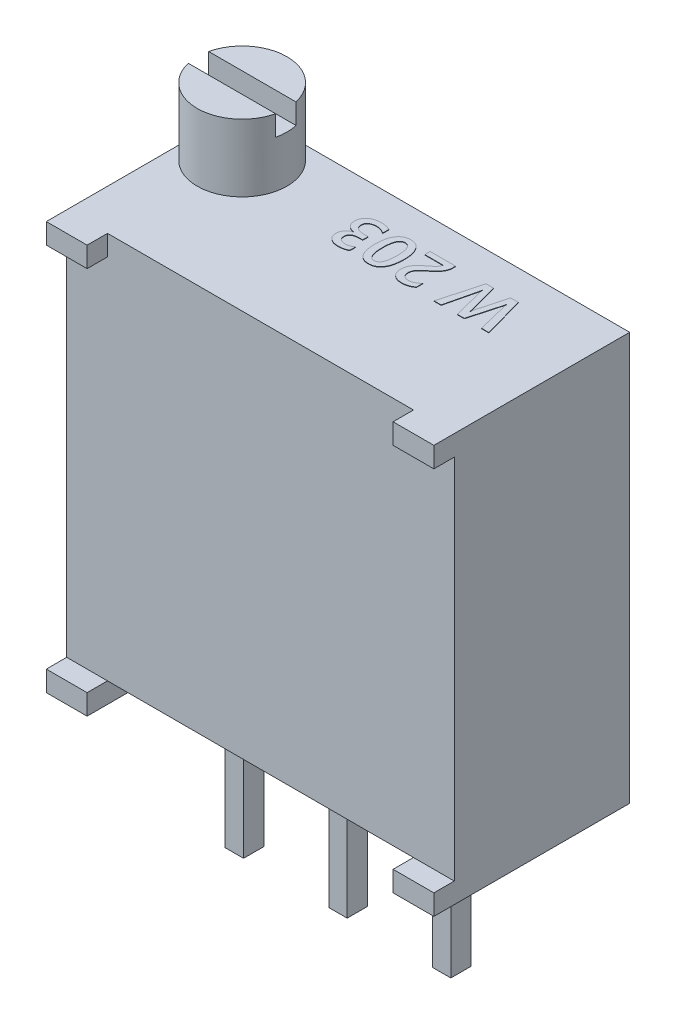
SolidWorks part; units mm, degrees
ref_plane "Front Plane" through (0, 0, 0) normal (0, 0, 1) x (1, 0, 0)
ref_plane "Top Plane" through (0, 0, 0) normal (0, 1, 0) x (1, 0, 0)
ref_plane "Right Plane" through (0, 0, 0) normal (1, 0, 0) x (0, 0, -1)
sketch "Sketch1" plane through (0, 0, 0) normal (0, 0, 1) x (1, 0, 0)
  line L0 (0, 0) -> (0, -4.75) construction
  line L1 (-3.75, -4.75) -> (3.75, -4.75)
  line L2 (-4.75, -4.75) -> (-4.75, 4.75)
  line L3 (-4.75, 4.75) -> (4.75, 4.75)
  line L4 (4.75, -4.75) -> (4.75, 4.75)
  line L5 (-4.75, -4.75) -> (4.75, 4.75) construction
  line L6 (-4.75, 4.75) -> (4.75, -4.75) construction
  line L7 (4.75, -4.75) -> (4.75, -5.25)
  line L8 (-4.75, -4.75) -> (-4.75, -5.25)
  line L9 (-4.75, -5.25) -> (-3.75, -5.25)
  line L10 (-3.75, -4.75) -> (-3.75, -5.25)
  line L11 (4.75, -5.25) -> (3.75, -5.25)
  line L12 (3.75, -4.75) -> (3.75, -5.25)
  point P0 (0, 0)
  dimension "D1" = 9.5
  dimension "D2" = 9.5
  dimension "D3" = 1
  dimension "D4" = 0.5
extrude "Boss-Extrude1" add sketch "Sketch1" along normal blind 4.3
sketch "Sketch2" plane through (0, 0, 4.3) normal (0, 0, 1) x (1, 0, 0)
  line L1 (-4.75, -5.25) -> (-3.75, -5.25)
  line L2 (-4.75, -5.25) -> (-4.75, -4.75)
  line L3 (-4.75, -4.75) -> (-3.75, -4.75)
  line L4 (-3.75, -5.25) -> (-3.75, -4.75)
  line L5 (4.75, -5.25) -> (3.75, -5.25)
  line L6 (4.75, -5.25) -> (4.75, -4.75)
  line L7 (4.75, -4.75) -> (3.75, -4.75)
  line L8 (3.75, -5.25) -> (3.75, -4.75)
  line L9 (-4.75, 4.75) -> (-3.75, 4.75)
  line L10 (-4.75, 4.75) -> (-4.75, 4.25)
  line L11 (-4.75, 4.25) -> (-3.75, 4.25)
  line L12 (-3.75, 4.75) -> (-3.75, 4.25)
  line L13 (4.75, 4.75) -> (3.75, 4.75)
  line L14 (4.75, 4.75) -> (4.75, 4.25)
  line L15 (4.75, 4.25) -> (3.75, 4.25)
  line L16 (3.75, 4.75) -> (3.75, 4.25)
  dimension "D1" = 0.5
  dimension "D2" = 0.5
extrude "Boss-Extrude2" add sketch "Sketch2" along normal blind 0.5
sketch "Sketch3" plane through (0, -4.75, 0) normal (0, -1, 0) x (1, 0, 0)
  line L0 (0, 2.15) -> (3.75, 2.15) construction
  line L1 (-0.225, 1.9) -> (0.225, 1.9)
  line L2 (-0.225, 1.9) -> (-0.225, 2.4)
  line L3 (-0.225, 2.4) -> (0.225, 2.4)
  line L4 (0.225, 1.9) -> (0.225, 2.4)
  line L5 (-0.225, 1.9) -> (0.225, 2.4) construction
  line L6 (-0.225, 2.4) -> (0.225, 1.9) construction
  line L7 (3.75, 4.3) -> (3.75, 0) construction
  line L8 (0, 0) -> (0, 2.15) construction
  line L9 (-3.75, 0) -> (3.75, 0) construction
  line L10 (2.315, 1.9) -> (2.765, 1.9)
  line L11 (2.315, 1.9) -> (2.315, 2.4)
  line L12 (2.315, 2.4) -> (2.765, 2.4)
  line L13 (2.765, 1.9) -> (2.765, 2.4)
  line L14 (2.315, 1.9) -> (2.765, 2.4) construction
  line L15 (2.315, 2.4) -> (2.765, 1.9) construction
  line L16 (-0.225, 1.9) -> (0.225, 1.9) [skipped]
  line L17 (-0.225, 1.9) -> (-0.225, 2.4) [skipped]
  line L18 (-0.225, 2.4) -> (0.225, 2.4) [skipped]
  line L19 (0.225, 1.9) -> (0.225, 2.4) [skipped]
  line L20 (-0.225, 1.9) -> (0.225, 2.4) construction
  line L21 (-0.225, 2.4) -> (0.225, 1.9) construction
  line L22 (-2.765, 1.9) -> (-2.315, 1.9)
  line L23 (-2.765, 1.9) -> (-2.765, 2.4)
  line L24 (-2.765, 2.4) -> (-2.315, 2.4)
  line L25 (-2.315, 1.9) -> (-2.315, 2.4)
  line L26 (-2.765, 1.9) -> (-2.315, 2.4) construction
  line L27 (-2.765, 2.4) -> (-2.315, 1.9) construction
  point P0 (0, 2.15)
  point P15 (2.54, 2.15)
  point P20 (0, 2.15)
  point P25 (-2.54, 2.15)
  dimension "D1" = 0.5
  dimension "D2" = 0.45
  dimension "D3" = 2
  dimension "D4" = 2
extrude "Boss-Extrude3" add sketch "Sketch3" along normal blind 4 separate body
sketch "Sketch4" plane through (0, 4.75, 0) normal (0, 1, 0) x (1, 0, 0)
  line L0 (4.75, 0) -> (-4.75, 0) construction
  line L1 (-4.75, -4.8) -> (-4.75, 0) construction
  circle A0 centre (-3.65, -1.1) radius 1.1
  dimension "D1" = 2.2
extrude "Boss-Extrude4" add sketch "Sketch4" along normal blind 1.65 separate body
sketch "Sketch5" plane through (0, 6.4, 0) normal (0, 1, 0) x (1, 0, 0)
  line L1 (-4.9, -1.35) -> (-2.4, -1.35)
  line L2 (-4.9, -1.35) -> (-4.9, -0.85)
  line L3 (-4.9, -0.85) -> (-2.4, -0.85)
  line L4 (-2.4, -1.35) -> (-2.4, -0.85)
  line L5 (-4.9, -1.35) -> (-2.4, -0.85) construction
  line L6 (-4.9, -0.85) -> (-2.4, -1.35) construction
  point P0 (-3.65, -1.1)
  dimension "D1" = 0.5
  dimension "D2" = 2.5
extrude "Cut-Extrude1" cut sketch "Sketch5" against normal blind 0.5
sketch "Sketch6" plane through (0, 4.75, 0) normal (0, 1, 0) x (1, 0, 0)
  line L0 (3.4447, -0.7408) -> (-1.349, -0.7408) construction
  text T0 "<b>W 203</b>" font "Yu Gothic UI" height 1
extrude "Boss-Extrude5" add sketch "Sketch6" along normal blind 0.01
sketch "Sketch7" plane through (0, 0, 0) normal (0, 0, -1) x (-1, 0, 0)
  line L0 (-3.0218, 0.8684) -> (3.3143, 0.8684) construction
  text T0 "<b>TRIMMER </b>\r\n<b>20k Ohm</b>" font "Century Gothic" height 1
  point P3 (-3.3905, 1.4215)
  point P4 (-3.1559, 1.2204)
  point P5 (-3.0218, 0.9522)
  point P6 (3.3143, 0.9019)
  point P7 (-2.9212, 0.8516)
extrude "Boss-Extrude6" add sketch "Sketch7" along normal blind 0.01
